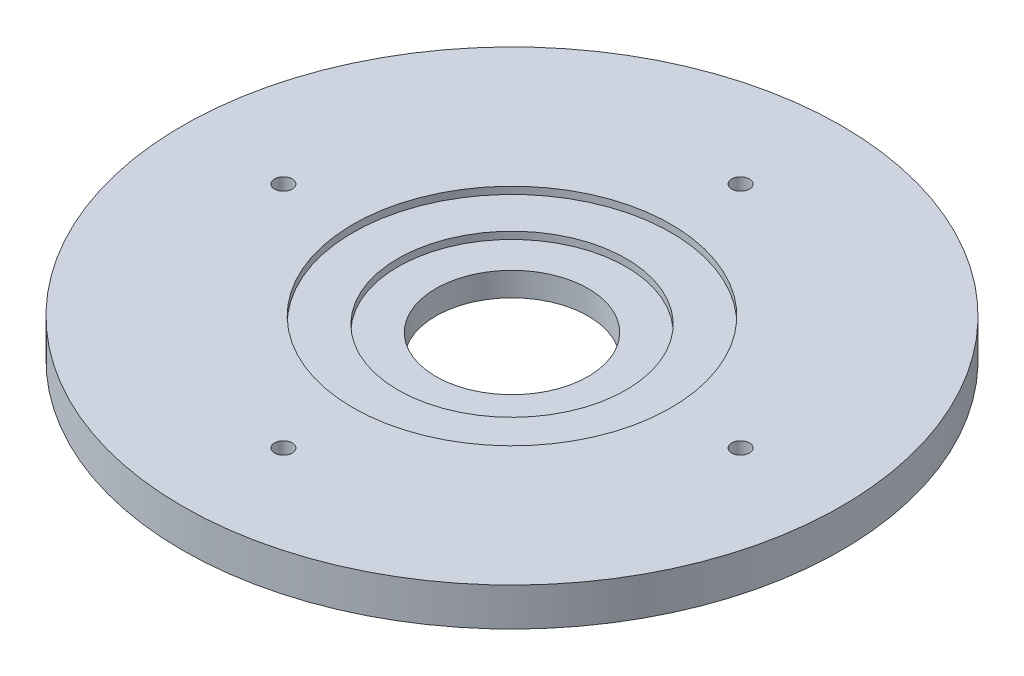
SolidWorks part; units mm, degrees
ref_plane "Front Plane" through (0, 0, 0) normal (0, 0, 1) x (1, 0, 0)
ref_plane "Top Plane" through (0, 0, 0) normal (0, 1, 0) x (1, 0, 0)
ref_plane "Right Plane" through (0, 0, 0) normal (1, 0, 0) x (0, 0, -1)
sketch "Sketch1" plane through (0, 0, 0) normal (0, 1, 0) x (1, 0, 0)
  circle A0 centre (0, 0) radius 54.9275
  circle A1 centre (0, 0) radius 12.7
  dimension "D1" = 109.855
  dimension "D2" = 25.4
extrude "Boss-Extrude1" add sketch "Sketch1" along normal blind 6.35
sketch "Sketch2" plane through (0, 6.35, 0) normal (0, 1, 0) x (1, 0, 0)
  circle A0 centre (0, 0) radius 26.5
  dimension "D1" = 53
extrude "Cut-Extrude1" cut sketch "Sketch2" against normal blind 1.1906
sketch "Sketch3" plane through (0, 6.35, 0) normal (0, 1, 0) x (1, 0, 0)
  circle A0 centre (0, 0) radius 19
  dimension "D1" = 38
extrude "Cut-Extrude2" cut sketch "Sketch3" against normal blind 2.3813
sketch "Sketch4" plane through (0, 6.35, 0) normal (0, 1, 0) x (-1, 0, 0)
  circle A0 centre (-38.1, 0) radius 1.4732
  circle A1 centre (0, -38.1) radius 1.4732
  circle A2 centre (38.1, 0) radius 1.4732
  circle A3 centre (0, 38.1) radius 1.4732
  dimension "D2" = 2.9464
  dimension "D1" = 38.1
  dimension "D3" = 38.1
  dimension "D4" = 38.1
  dimension "D5" = 38.1
extrude "Cut-Extrude3" cut sketch "Sketch4" against normal through all
